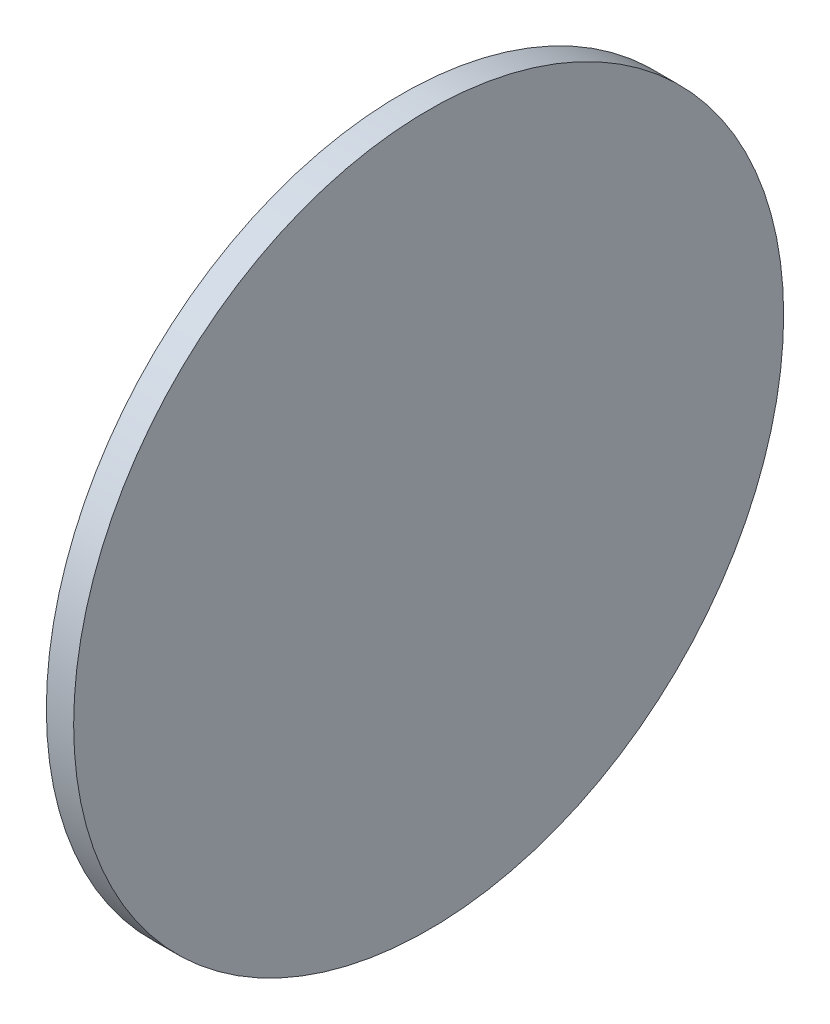
SolidWorks part; units mm, degrees
ref_plane "Front Plane" through (0, 0, 0) normal (0, 0, 1) x (1, 0, 0)
ref_plane "Top Plane" through (0, 0, 0) normal (0, 1, 0) x (1, 0, 0)
ref_plane "Right Plane" through (0, 0, 0) normal (1, 0, 0) x (0, 0, -1)
sketch "Sketch1" plane through (0, 0, 0) normal (1, 0, 0) x (0, 0, -1)
  circle A0 centre (0, 0) radius 330.2
  dimension "D1" = 660.4
extrude "Boss-Extrude1" add sketch "Sketch1" along normal blind 25.4 contours A0
